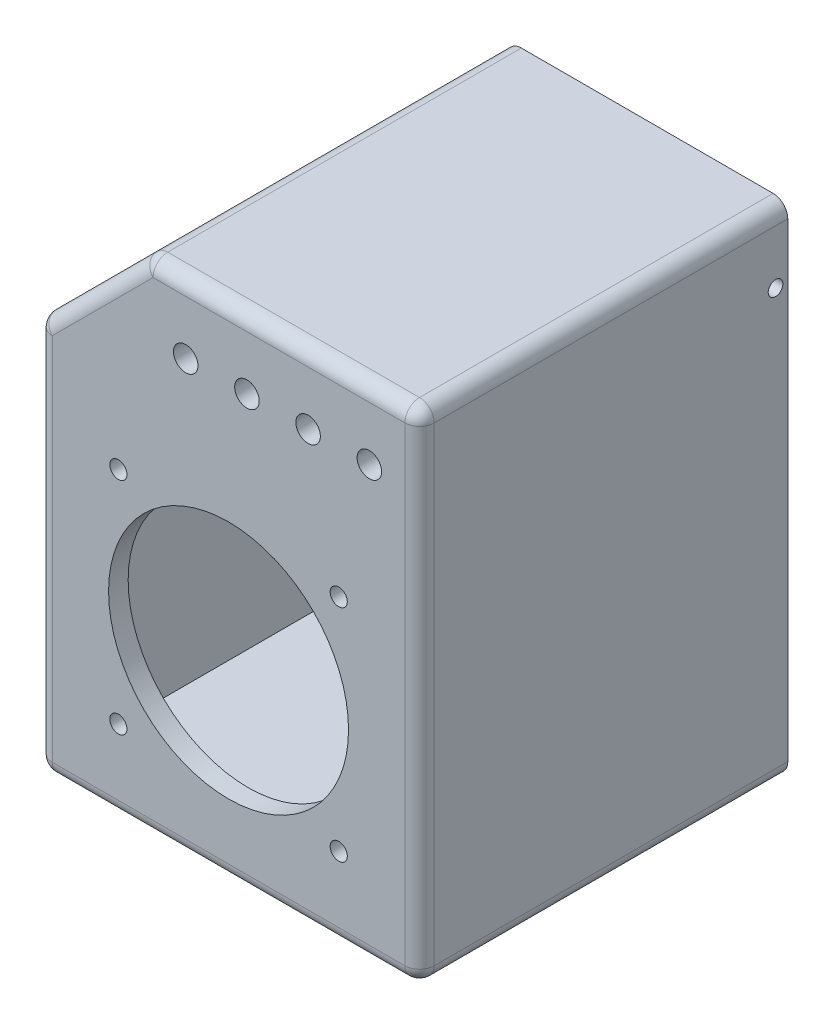
SolidWorks part; units mm, degrees
ref_plane "Alzado" through (0, 0, 0) normal (0, 0, 1) x (1, 0, 0)
ref_plane "Planta" through (0, 0, 0) normal (0, 1, 0) x (1, 0, 0)
ref_plane "Vista lateral" through (0, 0, 0) normal (1, 0, 0) x (0, 0, -1)
sketch "Croquis1" plane through (0, 0, 0) normal (0, 0, 1) x (1, 0, 0)
  line L0 (-39, 39) -> (39, 39)
  line L1 (-35, 35) -> (35, 35)
  line L2 (-35, 35) -> (-35, -35)
  line L3 (-35, -35) -> (35, -35)
  line L4 (35, 35) -> (35, -35)
  line L5 (-35, 35) -> (35, -35) construction
  line L6 (-35, -35) -> (35, 35) construction
  line L7 (39, 39) -> (39, -39)
  line L8 (-39, -39) -> (39, -39)
  line L9 (-39, 39) -> (-39, -39)
  circle A0 centre (0, 0) radius 24.5
  dimension "D1" = 49
  dimension "D2" = 70
  dimension "D3" = 70
  dimension "D4" = 4
extrude "Saliente-Extruir1" add sketch "Croquis1" along normal blind 4 contours L0 L9 L8 L7 L1 L4 L3 L2 | A0
sketch "Croquis2" plane through (0, 0, 0) normal (0, 0, -1) x (-1, 0, 0)
  line L0 (-35, 35) -> (-35, -35)
  line L1 (-39, 39) -> (39, 39)
  line L2 (-39, 39) -> (-39, -39)
  line L3 (-39, -39) -> (39, -39)
  line L4 (39, 39) -> (39, -39)
  line L5 (-35, -35) -> (35, -35)
  line L6 (35, 35) -> (35, -35)
  line L7 (-35, 35) -> (35, 35)
  dimension "D1" = 4
extrude "Saliente-Extruir2" add sketch "Croquis2" along normal blind 65
sketch "Croquis3" plane through (0, 0, -65) normal (0, 0, -1) x (-1, 0, 0)
  line L0 (35, -35) -> (35, 35) construction
  line L1 (35, -27) -> (39, -27)
  line L2 (35, -27) -> (35, 3.5)
  line L3 (35, 3.5) -> (39, 3.5)
  line L4 (39, -27) -> (39, 3.5)
  line L5 (39, -39) -> (39, 39) construction
  dimension "D1" = 8
  dimension "D2" = 30.5
extrude "Cortar-Extruir1" cut sketch "Croquis3" against normal blind 10.5
sketch "Croquis4" plane through (-39, 0, 0) normal (-1, 0, 0) x (0, 0, 1)
  line L1 (-50.5, -2) -> (-45, -2)
  line L2 (-50.5, -2) -> (-50.5, -6)
  line L3 (-50.5, -6) -> (-45, -6)
  line L4 (-45, -2) -> (-45, -6)
  line L6 (-50.5, -17.5) -> (-45, -17.5)
  line L7 (-50.5, -17.5) -> (-50.5, -21.5)
  line L8 (-50.5, -21.5) -> (-45, -21.5)
  line L9 (-45, -17.5) -> (-45, -21.5)
  line L10 (4, 39) -> (4, -39) construction
  dimension "D1" = 5.5
  dimension "D2" = 4
  dimension "D3" = 5.5
  dimension "D4" = 4
  dimension "D5" = 5.5
  dimension "D6" = 5.5
  dimension "D7" = 49
  dimension "D8" = 49
extrude "Cortar-Extruir2" cut sketch "Croquis4" along direction (1, 0, 0) on the side against the normal up to surface (4 mm away)
sketch "Croquis5" plane through (-39, 0, 0) normal (-1, 0, 0) x (0, 0, 1)
  line L0 (-50.5, -27) -> (-50.5, 3.5)
  line L1 (-50.5, 3.5) -> (-61, 3.5)
  line L2 (-61, 3.5) -> (-61, -27)
  line L3 (-50.5, -27) -> (-61, -27)
  dimension "D1" = 10.5
extrude "Cortar-Extruir3" cut sketch "Croquis5" against normal up to surface (4 mm away) up to face at (-35, -4, -47.75)
sketch "Croquis6" plane through (0, 0, 4) normal (0, 0, 1) x (1, 0, 0)
  line L1 (-39, 39) -> (39, 39)
  line L2 (-39, 39) -> (-39, 63)
  line L3 (-39, 63) -> (39, 63)
  line L4 (39, 39) -> (39, 63)
  dimension "D1" = 24
extrude "Saliente-Extruir3" add sketch "Croquis6" against normal blind 4
sketch "Croquis7" plane through (0, 0, 0) normal (0, 0, -1) x (-1, 0, 0)
  line L0 (-39, 39) -> (-39, 63)
  line L1 (-39, 63) -> (39, 63)
  line L2 (39, 63) -> (39, 39)
  line L3 (-35, 39) -> (-35, 59)
  line L4 (-35, 59) -> (35, 59)
  line L5 (35, 59) -> (35, 39)
  line L6 (-39, 39) -> (-35, 39)
  line L7 (35, 39) -> (39, 39)
  dimension "D1" = 4
extrude "Saliente-Extruir4" add sketch "Croquis7" along normal up to surface (65 mm away) up to face at (-12.3333, -3.9167, -65)
sketch "Croquis8" plane through (0, 0, -65) normal (0, 0, -1) x (-1, 0, 0)
  line L1 (35, 39) -> (-35, 39)
  line L2 (35, 39) -> (35, 35)
  line L3 (35, 35) -> (-35, 35)
  line L4 (-35, 39) -> (-35, 35)
extrude "Cortar-Extruir4" cut sketch "Croquis8" against normal blind 30
sketch "Croquis9" plane through (0, 0, 0) normal (0, 0, -1) x (-1, 0, 0)
  line L0 (-35, 39) -> (35, 59) construction
  line L1 (-35, 59) -> (35, 39) construction
  line L3 (-10, 49) -> (-16.25, 49) construction
  line L4 (-39, 63) -> (-39, -39) construction
  circle A0 centre (-16.25, 49) radius 2.5
  circle A1 centre (-3.75, 49) radius 2.5
  circle A2 centre (8.75, 49) radius 2.5
  circle A3 centre (-28.75, 49) radius 2.5
  dimension "D2" = 3
  dimension "D1" = 6.25
  dimension "D4" = 22.75
  dimension "D3" = 2
extrude "Cortar-Extruir5" cut sketch "Croquis9" against normal up to surface (4 mm away) up to face at (0, 12, 4)
sketch "Croquis11" plane through (0, 0, 4) normal (0, 0, 1) x (1, 0, 0)
  line L1 (-22.5, 22.5) -> (22.5, 22.5) construction
  line L2 (-22.5, 22.5) -> (-22.5, -22.5) construction
  line L3 (-22.5, -22.5) -> (22.5, -22.5) construction
  line L4 (22.5, 22.5) -> (22.5, -22.5) construction
  line L5 (-22.5, 22.5) -> (22.5, -22.5) construction
  line L6 (-22.5, -22.5) -> (22.5, 22.5) construction
  circle A0 centre (-22.5, 22.5) radius 1.75
  circle A1 centre (22.5, 22.5) radius 1.75
  circle A2 centre (22.5, -22.5) radius 1.75
  circle A3 centre (-22.5, -22.5) radius 1.75
  point P0 (0, 0)
  dimension "D3" = 3.5
  dimension "D1" = 45
  dimension "D2" = 45
  dimension "D4" = 2
  dimension "D5" = 2
extrude "Cortar-Extruir7" cut sketch "Croquis11" against normal up to surface (4 mm away) up to face at (0, 0, 0)
sketch "Croquis12" plane through (0, 0, -65) normal (0, 0, -1) x (-1, 0, 0)
  line L0 (39, 3.5) -> (39, 63)
  line L1 (39, 63) -> (-39, 63)
  line L2 (-39, 63) -> (-39, -39)
  line L3 (-39, -39) -> (39, -39)
  line L4 (39, -39) -> (39, -27)
  line L5 (39, -27) -> (35, -27)
  line L6 (35, -27) -> (35, -35)
  line L7 (35, -35) -> (-35, -35)
  line L8 (-35, -35) -> (-35, 59)
  line L9 (-35, 59) -> (35, 59)
  line L10 (35, 59) -> (35, 3.5)
  line L11 (35, 3.5) -> (39, 3.5)
extrude "Saliente-Extruir5" add sketch "Croquis12" along normal blind 6.2
sketch "Croquis13" plane through (-39, 0, 0) normal (-1, 0, 0) x (0, 0, 1)
  circle A0 centre (-68.7, 49) radius 1.5
extrude "Cortar-Extruir8" cut sketch "Croquis13" against normal up to surface (78 mm away) up to face at (39, 12, -33.6)
sketch "Croquis15" plane through (0, -39, 0) normal (0, -1, 0) x (1, 0, 0)
  circle A0 centre (0, -68.7) radius 1.5
extrude "Cortar-Extruir9" cut sketch "Croquis15" against normal blind 10
sketch "Croquis18" plane through (0, 0, 0) normal (0, 0, -1) x (-1, 0, 0)
  line L0 (37.8284, 41.8284) -> (46.1808, 33.476)
  line L1 (37.8284, 41.8284) -> (7.0609, 72.5959)
  line L2 (46.1808, 33.476) -> (52.6545, 70.8091)
  line L3 (52.6545, 70.8091) -> (7.0609, 72.5959)
extrude "Cortar-Extruir10" cut sketch "Croquis18" against normal through all both and the other way through all
sketch "Croquis19" plane through (0, 0, 0) normal (0, 0, -1) x (-1, 0, 0)
  line L0 (35, 39) -> (15, 59)
  line L1 (-35, 59) -> (20.6569, 59) construction
  line L2 (15, 59) -> (20.6569, 59)
  line L3 (20.6569, 59) -> (35, 44.6569)
  line L4 (35, 44.6569) -> (35, 39)
extrude "Saliente-Extruir12" add sketch "Croquis19" along normal up to surface (71.2 mm away) up to face at (-3.7314, 4.2, -71.2)
sketch "Croquis20" plane through (-39.8284, 39.8284, 0) normal (-0.7071, 0.7071, 0) x (0, 0, 1)
  line L0 (-6, 18.9706) -> (-21, 18.9706) construction
  line L5 (-8, 15.4706) -> (-4, 15.4706)
  line L6 (-8, 15.4706) -> (-8, 22.4706)
  line L7 (-8, 22.4706) -> (-4, 22.4706)
  line L8 (-4, 15.4706) -> (-4, 22.4706)
  line L9 (-8, 15.4706) -> (-4, 22.4706) construction
  line L10 (-8, 22.4706) -> (-4, 15.4706) construction
  line L11 (-21, 18.9706) -> (-36, 18.9706) construction
  line L12 (-36, 18.9706) -> (-56, 18.9706) construction
  line L13 (4, 32.7696) -> (4, 1.1716) construction
  circle A0 centre (-21, 18.9706) radius 3.7
  circle A1 centre (-36, 18.9706) radius 3.7
  circle A2 centre (-56, 18.9706) radius 3
  point P0 (-6, 18.9706)
  point P14 (4, 16.9706)
  dimension "D4" = 7.4
  dimension "D6" = 7.4
  dimension "D9" = 6
  dimension "D1" = 7
  dimension "D2" = 4
  dimension "D3" = 15
  dimension "D5" = 15
  dimension "D7" = 20
  dimension "D8" = 10
  dimension "D10" = 2
extrude "Cortar-Extruir11" cut sketch "Croquis20" against normal up to surface (4 mm away) up to face at (-27, 47, -35.48)
sketch "Croquis21" plane through (-37, 37, 0) normal (0.7071, -0.7071, 0) x (0, 0, -1)
  line L1 (52, 12.4706) -> (60, 12.4706)
  line L2 (52, 12.4706) -> (52, 25.4706)
  line L3 (52, 25.4706) -> (60, 25.4706)
  line L4 (60, 12.4706) -> (60, 25.4706)
  line L5 (52, 12.4706) -> (60, 25.4706) construction
  line L6 (52, 25.4706) -> (60, 12.4706) construction
  point P0 (56, 18.9706)
  dimension "D1" = 13
  dimension "D2" = 8
extrude "Cortar-Extruir12" cut sketch "Croquis21" against normal blind 1.5
sketch "Croquis22" plane through (-39.8284, 39.8284, 0) normal (-0.7071, 0.7071, 0) x (0, 0, 1)
  line L0 (-71.2, 16.9706) -> (-68.7, 16.9706) construction
  line L1 (-71.2, 32.7696) -> (-71.2, 1.1716) construction
  circle A0 centre (-68.7, 16.9706) radius 1.5
  dimension "D2" = 3
  dimension "D1" = 2.5
extrude "Cortar-Extruir13" cut sketch "Croquis22" against normal up to surface (4 mm away) up to face at (-23.5858, 50.4142, -56)
fillet "Redondeo1" radius 3 10 edges at (-16.6569, 63, -33.6) (11.1716, 63, 4) (39, 63, -33.6) (39, 12, 4) (39, -39, -33.6) (0, -39, 4) (-39, -39, -33.6) (-39, 0.8284, 4) (-39, 40.6569, -33.6) (-27.8284, 51.8284, 4)
